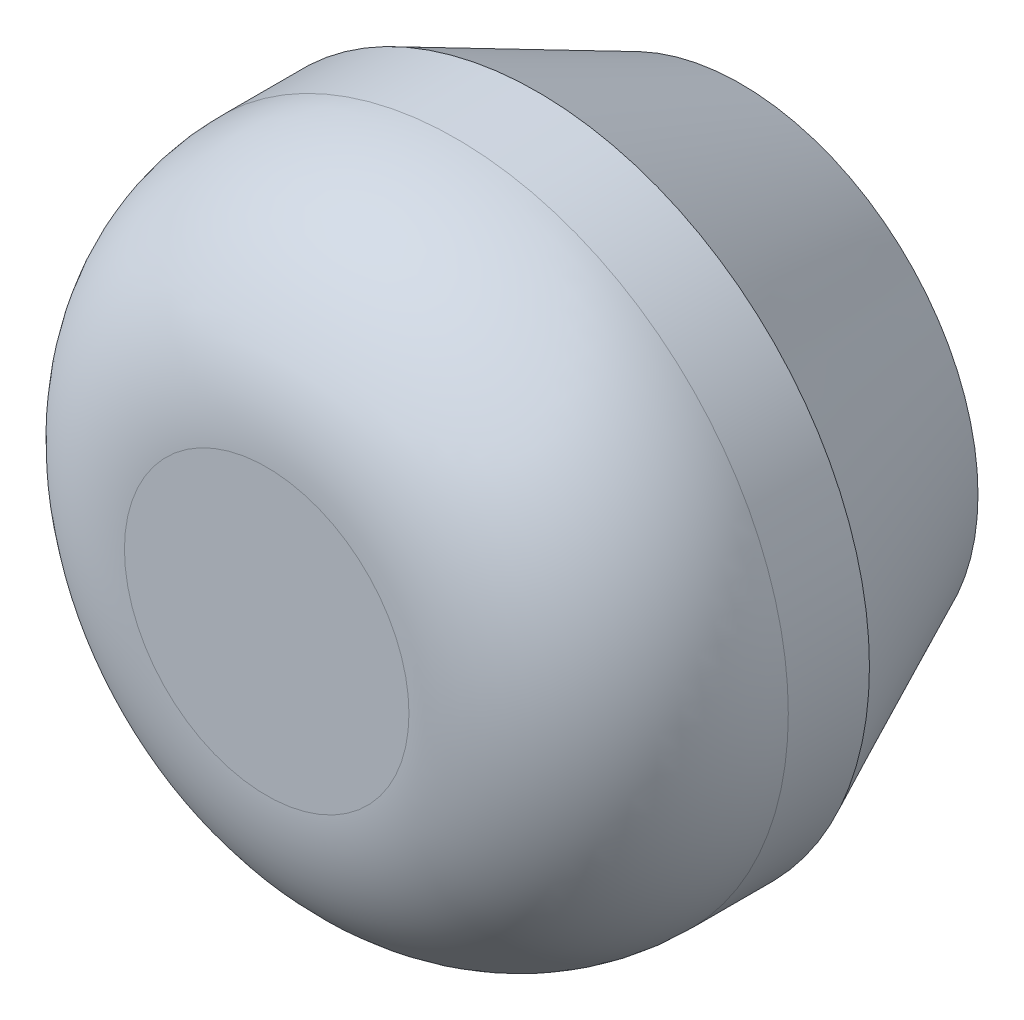
SolidWorks part; units mm, degrees
ref_plane "Спереди" through (0, 0, 0) normal (0, 0, 1) x (1, 0, 0)
ref_plane "Сверху" through (0, 0, 0) normal (0, 1, 0) x (1, 0, 0)
ref_plane "Справа" through (0, 0, 0) normal (1, 0, 0) x (0, 0, -1)
sketch "Эскиз1" plane through (0, 0, 0) normal (0, 0, 1) x (1, 0, 0)
  circle A0 centre (0, 0) radius 3.5
extrude "Бобышка-Вытянуть1" add sketch "Эскиз1" along normal blind 5
fillet "Скругление1" radius 2 1 edges at (3.5, 0, 5)
sketch "Эскиз2" plane through (0, 0, 0) normal (0, 0, -1) x (-1, 0, 0)
  line L1 (-1.3, 1.3) -> (1.3, 1.3)
  line L2 (-1.3, 1.3) -> (-1.3, -1.3)
  line L3 (-1.3, -1.3) -> (1.3, -1.3)
  line L4 (1.3, 1.3) -> (1.3, -1.3)
  line L5 (-1.3, 1.3) -> (1.3, -1.3) construction
  line L6 (-1.3, -1.3) -> (1.3, 1.3) construction
  point P0 (0, 0)
  dimension "D1" = 2.6
extrude "Вырез-Вытянуть1" cut sketch "Эскиз2" against normal blind 4
chamfer "Фаска1" distance 1 angle 65 1 edges at (3.5, 0, 0)
